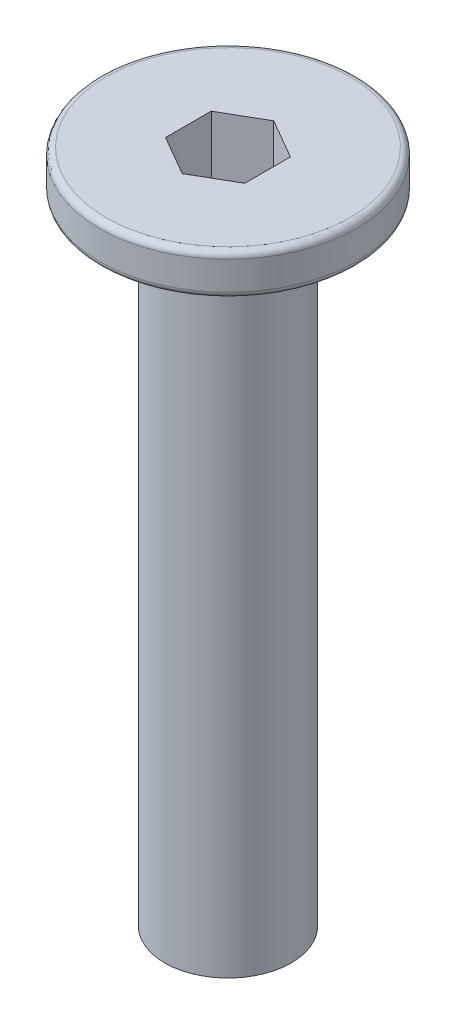
SolidWorks part; units mm, degrees
ref_plane "Front Plane" through (0, 0, 0) normal (0, 0, 1) x (1, 0, 0)
ref_plane "Top Plane" through (0, 0, 0) normal (0, 1, 0) x (1, 0, 0)
ref_plane "Right Plane" through (0, 0, 0) normal (1, 0, 0) x (0, 0, -1)
sketch "Sketch1" plane through (0, 0, 0) normal (0, 1, 0) x (1, 0, 0)
  circle A0 centre (0, 0) radius 4.05
  dimension "D1" = 8.1
extrude "Boss-Extrude1" add sketch "Sketch1" along normal blind 1.3
fillet "Fillet1" radius 0.2 2 edges at (0, 0, 4.05) (0, 1.3, 4.05)
sketch "Sketch2" plane through (0, 0, 0) normal (0, -1, 0) x (1, 0, 0)
  circle A0 centre (0, 0) radius 2
  dimension "D1" = 4
extrude "Boss-Extrude2" add sketch "Sketch2" along normal blind 20
sketch "Sketch3" plane through (0, 1.3, 0) normal (0, 1, 0) x (1, 0, 0)
  line L1 (-1.25, -0.7217) -> (0, -1.4434)
  line L2 (0, -1.4434) -> (1.25, -0.7217)
  line L3 (1.25, -0.7217) -> (1.25, 0.7217)
  line L4 (1.25, 0.7217) -> (0, 1.4434)
  line L5 (0, 1.4434) -> (-1.25, 0.7217)
  line L6 (-1.25, 0.7217) -> (-1.25, -0.7217)
  circle A0 centre (0, 0) radius 1.25 construction
  dimension "D1" = 2.5
extrude "Cut-Extrude1" cut sketch "Sketch3" against normal blind 2
